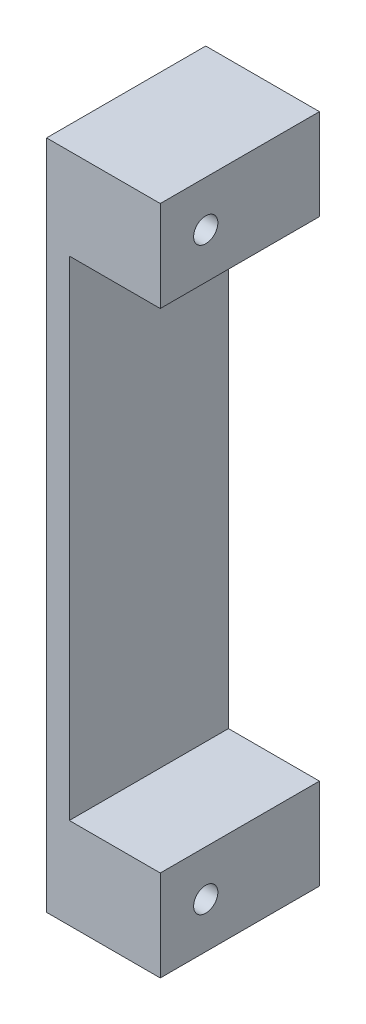
SolidWorks part; units mm, degrees
material "6061 Alloy"
ref_plane "Front Plane" through (0, 0, 0) normal (0, 0, 1) x (1, 0, 0)
ref_plane "Top Plane" through (0, 0, 0) normal (0, 1, 0) x (1, 0, 0)
ref_plane "Right Plane" through (0, 0, 0) normal (1, 0, 0) x (0, 0, -1)
sketch "Sketch1" plane through (0, 0, 0) normal (1, 0, 0) x (0, 0, -1)
  line L1 (0, 0) -> (17.78, 0)
  line L2 (0, 0) -> (0, 74.93)
  line L3 (0, 74.93) -> (17.78, 74.93)
  line L4 (17.78, 0) -> (17.78, 74.93)
  dimension "D1" = 17.78
  dimension "D2" = 74.93
extrude "Boss-Extrude1" add sketch "Sketch1" along normal blind 12.7
sketch "Sketch2" plane through (12.7, 0, 0) normal (1, 0, 0) x (0, 0, -1)
  line L0 (0, 74.93) -> (0, 0) construction
  line L1 (0, 64.77) -> (10.16, 64.77)
  line L2 (0, 64.77) -> (0, 10.16)
  line L3 (0, 10.16) -> (10.16, 10.16)
  line L4 (13.97, 64.77) -> (24.13, 64.77)
  line L6 (17.78, 74.93) -> (0, 74.93) construction
  line L7 (0, 0) -> (17.78, 0) construction
  line L8 (13.97, 10.16) -> (24.13, 10.16)
  line L9 (24.13, 10.16) -> (24.13, 64.77)
  line L16 (13.97, 64.77) -> (10.16, 64.77)
  line L17 (13.97, 10.16) -> (10.16, 10.16)
  dimension "D1" = 10.16
  dimension "D2" = 10.16
extrude "Cut-Extrude1" cut sketch "Sketch2" against normal blind 10.16
hole_wizard "Tap Drill for #6-32 Tap1" positions "Sketch4" profile "Sketch3" hole size "#6-32" standard "ANSI Inch" end condition through all
sketch "Sketch4" plane through (12.7, 0, 0) normal (1, 0, 0) x (0, 0, -1)
  line L15 (17.78, 74.93) -> (0, 74.93) construction
  line L16 (0, 74.93) -> (0, 64.77) construction
  line L17 (0, 10.16) -> (0, 0) construction
  line L19 (0, 0) -> (17.78, 0) construction
  point P33 (5.08, 69.85)
  point P39 (5.08, 5.08)
  dimension "D1" = 5.08
  dimension "D2" = 5.08
  dimension "D3" = 5.08
  dimension "D4" = 5.08
sketch "Sketch3" plane through (12.7, 69.85, -5.08) normal (0, 1, 0) x (0, 0, -1)
  line L0 (0, 0) -> (0, 12.7)
  line L1 (0, 12.7) -> (1.3525, 12.7)
  line L2 (1.3525, 12.7) -> (1.3525, 0)
  line L5 (1.3525, 0) -> (0, 0)
  line L11 (0, -6.35) -> (0, 107.95) construction
  dimension "Thru Hole Dia." = 2.7051
  dimension "Thru Hole Depth" = 12.7
sketch "Sketch5" plane through (0, 0, -17.78) normal (0, 0, -1) x (-1, 0, 0)
  line L0 (-12.7, 64.77) -> (0, 74.93) construction
  line L1 (0, 74.93) -> (-12.7, 74.93) construction
  line L2 (-12.7, 74.93) -> (0, 64.77) construction
  line L3 (0, 0) -> (0, 74.93) construction
  line L4 (0, 64.77) -> (0, 37.465) construction
  line L5 (0, 37.465) -> (-2.54, 37.465) construction
  line L6 (-2.54, 10.16) -> (-2.54, 64.77) construction
  line L7 (-6.35, 0) -> (-6.35, 10.16) construction
  line L8 (-12.7, 0) -> (0, 0) construction
  line L9 (-2.54, 10.16) -> (-12.7, 10.16) construction
  line L10 (-6.35, 4.953) -> (-6.35, 5.207) construction
  line L11 (-8.7439, 4.953) -> (-8.7439, 5.207)
  line L12 (-3.956, 4.953) -> (-3.956, 5.207)
  circle A0 centre (-6.35, 69.85) radius 2.394
  arc A1 (-8.7439, 4.953) -> (-3.956, 4.953) centre (-6.35, 4.953) ccw
  arc A2 (-3.956, 5.207) -> (-8.7439, 5.207) centre (-6.35, 5.207) ccw
  point P23 (-6.35, 5.08)
extrude "Cut-Extrude2" cut sketch "Sketch5" against normal blind 11.1125
